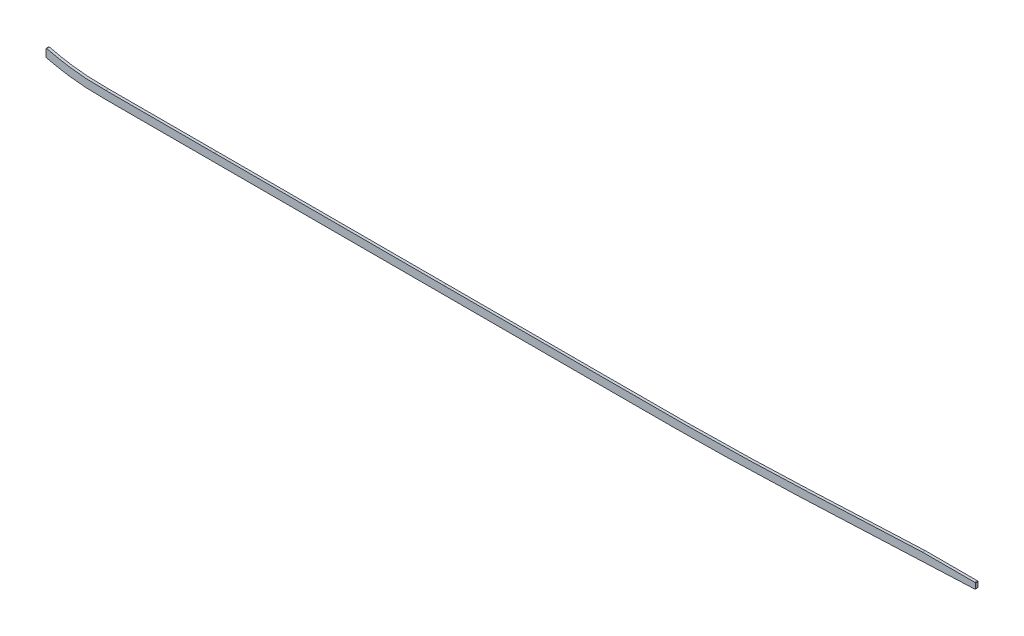
SolidWorks part; units mm, degrees
material "Plywood"
ref_plane "Front Plane" through (0, 0, 0) normal (0, 0, 1) x (1, 0, 0)
ref_plane "Top Plane" through (0, 0, 0) normal (0, 1, 0) x (1, 0, 0)
ref_plane "Right Plane" through (0, 0, 0) normal (1, 0, 0) x (0, 0, -1)
sketch "Sketch1" plane through (0, 0, 0) normal (0, 0, 1) x (1, 0, 0)
  line L0 (1046.2855, 53.4707) -> (499.61, 53.4707) construction
  line L1 (55, 0) -> (-55, 0) construction
  line L2 (1046.2855, -53.4707) -> (499.61, -53.4707)
  line L3 (1046.2855, -34.4207) -> (499.61, -34.4207)
  line L4 (99.06, -18.1493) -> (99.06, -37.7415)
  line L5 (2669.54, 9.5231) -> (2669.54, -9.569)
  spline S0 degree 5 poles (2699.7923, 7.5245) (2639.6368, 11.6572) (2579.4813, 15.4358) (2518.4981, 19.1485) (2436.3555, 23.2524) (2354.213, 26.6315) (2332.5703, 27.481) (2156.2686, 34.3778) (1979.9669, 41.6286) (1824.1143, 52.7713) (1636.9286, 53.5796) (1449.7429, 53.454) (1418.0067, 53.4707) (1324.8993, 53.4707) (1231.7919, 53.4707) (1170.4413, 53.4707) (1108.7841, 53.4707) (1047.1269, 53.4707) (1046.8464, 53.4707) (1046.5659, 53.4707) (1046.2855, 53.4707) knots 100.654805 100.654805 100.654805 100.654805 100.654805 100.654805 130.927897 130.927897 130.927897 141.337055 141.337055 141.337055 218.101815 218.101815 218.101815 233.772059 233.772059 233.772059 264.077723 264.077723 264.077723 264.216209 264.216209 264.216209 264.216209 264.216209 264.216209 weights 1 1 1 1 1 1 1 1 1 1 1 1 1 1 1 1 1 1 1 1 1 construction
  spline S1 degree 5 poles (499.61, 53.4707) (492.1368, 53.4707) (484.7543, 53.4707) (477.443, 53.4707) (448.5166, 53.4707) (419.5901, 53.4707) (398.3681, 53.4707) (355.6475, 53.4707) (312.927, 53.4707) (289.2351, 53.4703) (265.365, 53.4707) (241.4948, 53.4707) (241.4716, 53.4707) (241.4484, 53.4707) (241.4251, 53.4707) knots 19.90683 19.90683 19.90683 19.90683 19.90683 19.90683 23.637897 23.637897 23.637897 34.276546 34.276546 34.276546 46.401341 46.401341 46.401341 46.413154 46.413154 46.413154 46.413154 46.413154 46.413154 weights 1 1 1 1 1 1 1 1 1 1 1 1 1 1 1 construction
  spline S2 degree 5 poles (241.4251, 53.4707) (224.2869, 53.4707) (207.1495, 53.4673) (190.2039, 52.6866) (151.6561, 49.0319) (113.1083, 41.5037) (91.9499, 36.3426) (71.313, 30.9696) (50.6762, 24.7565) knots 0 0 0 0 0 0 8.713816 8.713816 8.713816 19.90683 19.90683 19.90683 19.90683 19.90683 19.90683 weights 1 1 1 1 1 1 1 1 1 construction
  spline S3 degree 5 poles (241.4251, -53.4707) (224.2869, -53.4707) (207.1495, -53.4673) (190.2039, -52.6866) (151.6561, -49.0319) (113.1083, -41.5037) (91.9499, -36.3426) (71.313, -30.9696) (50.6762, -24.7565) knots 0 0 0 0 0 0 8.713816 8.713816 8.713816 19.90683 19.90683 19.90683 19.90683 19.90683 19.90683 weights 1 1 1 1 1 1 1 1 1
  spline S4 degree 5 poles (499.61, -53.4707) (492.1368, -53.4707) (484.7543, -53.4707) (477.443, -53.4707) (448.5166, -53.4707) (419.5901, -53.4707) (398.3681, -53.4707) (355.6475, -53.4707) (312.927, -53.4707) (289.2351, -53.4703) (265.365, -53.4707) (241.4948, -53.4707) (241.4716, -53.4707) (241.4484, -53.4707) (241.4251, -53.4707) knots 19.90683 19.90683 19.90683 19.90683 19.90683 19.90683 23.637897 23.637897 23.637897 34.276546 34.276546 34.276546 46.401341 46.401341 46.401341 46.413154 46.413154 46.413154 46.413154 46.413154 46.413154 weights 1 1 1 1 1 1 1 1 1 1 1 1 1 1 1
  spline S5 degree 5 poles (2699.7923, -7.5245) (2639.6368, -11.6572) (2579.4813, -15.4358) (2518.4981, -19.1485) (2436.3555, -23.2524) (2354.213, -26.6315) (2332.5703, -27.481) (2156.2686, -34.3778) (1979.9669, -41.6286) (1824.1143, -52.7713) (1636.9286, -53.5796) (1449.7429, -53.454) (1418.0067, -53.4707) (1324.8993, -53.4707) (1231.7919, -53.4707) (1170.4413, -53.4707) (1108.7841, -53.4707) (1047.1269, -53.4707) (1046.8464, -53.4707) (1046.5659, -53.4707) (1046.2855, -53.4707) knots 100.654805 100.654805 100.654805 100.654805 100.654805 100.654805 130.927897 130.927897 130.927897 141.337055 141.337055 141.337055 218.101815 218.101815 218.101815 233.772059 233.772059 233.772059 264.077723 264.077723 264.077723 264.216209 264.216209 264.216209 264.216209 264.216209 264.216209 weights 1 1 1 1 1 1 1 1 1 1 1 1 1 1 1 1 1 1 1 1 1
  spline S6 degree 1 poles (2698.4867, 11.4807) (1046.2855, -34.4207) knots 0 0 1 1 construction
  spline S7 degree 1 poles (499.61, -34.4207) (241.4252, -34.4207) knots 0 0 1 1 construction
  spline S8 degree 1 poles (241.4252, -34.4207) (56.168, -6.5153) knots 0 0 1 1 construction
  spline S9 degree 3 poles (2698.4867, 11.4807) (2691.2474, 10.9833) (2679.1952, 10.1655) (2662.2765, 9.0388) (2635.6663, 7.2925) (2596.8577, 4.8261) (2545.7297, 1.7583) (2494.4053, -1.0986) (2451.533, -3.2666) (2417.1983, -4.8671) (2391.4571, -6.0036) (2365.6347, -7.0869) (2339.5463, -8.1377) (2313.4661, -9.1651) (2287.6124, -10.1795) (2261.7633, -11.201) (2227.2853, -12.5838) (2184.1756, -14.3661) (2132.4291, -16.6074) (2063.4255, -19.7089) (1977.1749, -23.7005) (1873.7325, -28.1494) (1770.3746, -31.6575) (1667.0857, -33.7931) (1581.0111, -34.3832) (1512.074, -34.4278) (1443.0615, -34.4095) (1356.8009, -34.4244) (1218.7946, -34.4185) (1115.289, -34.4207) (1046.2855, -34.4207) knots 100.654805 100.654805 100.654805 100.654805 102.842388 104.300777 105.766098 110.877392 115.988686 121.09998 126.211274 128.766921 131.322568 133.878215 136.433862 138.989509 141.545156 144.100803 146.656449 151.767743 156.879037 161.990331 172.212919 182.435507 192.658094 202.880682 213.10327 218.214564 223.325858 233.548445 243.771033 264.216209 264.216209 264.216209 264.216209
  spline S10 degree 3 poles (499.61, -34.4207) (488.6147, -34.4207) (472.2364, -34.4207) (449.9402, -34.4207) (427.7713, -34.4207) (405.8747, -34.4207) (384.5849, -34.4207) (368.9002, -34.4207) (353.3766, -34.4207) (332.6085, -34.4207) (306.2878, -34.4206) (274.0235, -34.4205) (252.271, -34.4207) (241.4252, -34.4207) knots 19.90683 19.90683 19.90683 19.90683 23.22012 24.876765 26.533411 29.846701 31.503346 33.159992 34.816637 36.473282 39.786573 43.099863 46.413154 46.413154 46.413154 46.413154
  spline S11 degree 3 poles (241.4252, -34.4207) (239.3949, -34.4207) (235.3223, -34.4205) (227.2744, -34.3987) (217.3194, -34.2975) (205.5307, -33.9764) (189.9633, -33.2126) (170.697, -31.5435) (147.5333, -28.3144) (125.4828, -24.2021) (107.4399, -20.1965) (92.2061, -16.4882) (75.9505, -12.2555) (63.6202, -8.7589) (56.168, -6.5153) knots 0 0 0 0 0.622088 1.244177 2.488354 3.732531 4.976707 7.465061 9.953415 12.441768 14.558235 15.802412 17.418476 19.90683 19.90683 19.90683 19.90683
  point P2 (0, 0)
  dimension "D1" = 50.6762
  dimension "D3" = 99.06
  dimension "D4" = 2669.54
  dimension "D2" = 19.05
extrude "Boss-Extrude1" add sketch "Sketch1" along normal mid plane 6.35 contours S10 S11 L4 S3 S4 L2 S5 L5 S9 L3
sketch "Sketch2" plane through (0, 0, 3.175) normal (0, 0, 1) x (1, 0, 0)
  line L0 (2185.533, -14.3257) -> (2311.4, -14.3257)
  line L1 (2311.4, -14.3257) -> (2311.4, -9.2457)
  line L2 (2311.4, -14.3257) -> (2311.4, -28.3104)
  line L3 (2669.54, 9.5231) -> (2669.54, -9.569) construction
  line L4 (2669.54, 9.5231) -> (2669.54, -9.569)
  spline S0 degree 3 poles (689.0175, 232.3189) (4033.8285, 148.9311) (3356.6623, 54.6077) (2635.6663, 7.2925) (2596.8577, 4.8261) (2545.7297, 1.7583) (2494.4053, -1.0986) (2451.533, -3.2666) (2417.1983, -4.8671) (2391.4571, -6.0036) (2365.6347, -7.0869) (2339.5463, -8.1377) (2313.4661, -9.1651) (2287.6124, -10.1795) (2261.7633, -11.201) (2227.2853, -12.5838) (2184.1756, -14.3661) (2132.4291, -16.6074) (2063.4255, -19.7089) (1977.1749, -23.7005) (1873.7325, -28.1494) (1770.3746, -31.6575) (1667.0857, -33.7931) (1581.0111, -34.3832) (1512.074, -34.4278) (1443.0615, -34.4095) (1356.8009, -34.4244) (551.9641, -34.3896) (-218.4198, -34.7282) (-953.6342, -29.9632) knots -106.828462 -106.828462 -106.828462 -106.828462 104.300777 105.766098 110.877392 115.988686 121.09998 126.211274 128.766921 131.322568 133.878215 136.433862 138.989509 141.545156 144.100803 146.656449 151.767743 156.879037 161.990331 172.212919 182.435507 192.658094 202.880682 213.10327 218.214564 223.325858 233.548445 243.771033 461.793666 461.793666 461.793666 461.793666 only from (2669.54, 9.5231) to (1046.2855, -34.4207) construction
  spline S1 degree 3 poles (2669.54, 9.5231) (2667.1265, 9.3624) (2659.8616, 8.8803) (2635.6663, 7.2925) (2596.8577, 4.8261) (2545.7297, 1.7583) (2494.4053, -1.0986) (2451.533, -3.2666) (2417.1983, -4.8671) (2391.4571, -6.0036) (2365.6347, -7.0869) (2339.5463, -8.1377) (2313.4661, -9.1651) (2287.6124, -10.1795) (2261.7633, -11.201) (2227.2853, -12.5838) (2184.1756, -14.3661) (2132.4291, -16.6074) (2063.4255, -19.7089) (1977.1749, -23.7005) (1873.7325, -28.1494) (1770.3746, -31.6575) (1667.0857, -33.7931) (1581.0111, -34.3832) (1512.074, -34.4278) (1443.0615, -34.4095) (1356.8009, -34.4244) (1218.7946, -34.4185) (1115.289, -34.4207) (1046.2855, -34.4207) knots 103.571583 103.571583 103.571583 103.571583 104.300777 105.766098 110.877392 115.988686 121.09998 126.211274 128.766921 131.322568 133.878215 136.433862 138.989509 141.545156 144.100803 146.656449 151.767743 156.879037 161.990331 172.212919 182.435507 192.658094 202.880682 213.10327 218.214564 223.325858 233.548445 243.771033 264.216209 264.216209 264.216209 264.216209
  spline S2 degree 5 poles (4524.4896, 699.6349) (3179.77, -69.42) (3083.4624, 36.6115) (2859.542, 1.0131) (2606.8775, -16.2376) (2354.213, -26.6315) (2332.5703, -27.481) (2156.2686, -34.3778) (1979.9669, -41.6286) (1824.1143, -52.7713) (1636.9286, -53.5796) (1449.7429, -53.454) (1418.0067, -53.4707) (1324.8993, -53.4707) (1231.7919, -53.4707) (1170.4413, -53.4707) (970.3038, -53.4707) (770.1663, -53.4707) (702.0423, -53.4707) (-16.6162, -53.4711) (3039.7057, -53.1927) knots 16.201417 16.201417 16.201417 16.201417 16.201417 16.201417 130.927897 130.927897 130.927897 141.337055 141.337055 141.337055 218.101815 218.101815 218.101815 233.772059 233.772059 233.772059 264.077723 264.077723 264.077723 332.592886 332.592886 332.592886 332.592886 332.592886 332.592886 weights 1 1 1 1 1 1 1 1 1 1 1 1 1 1 1 1 1 1 1 1 1 only from (2669.54, -9.569) to (1046.2855, -53.4707) construction
  spline S3 degree 5 poles (2669.54, -9.569) (2615.3936, -13.1707) (2561.0807, -16.5361) (2506.2052, -19.7586) (2430.2091, -23.5052) (2354.213, -26.6315) (2332.5703, -27.481) (2156.2686, -34.3778) (1979.9669, -41.6286) (1824.1143, -52.7713) (1636.9286, -53.5796) (1449.7429, -53.454) (1418.0067, -53.4707) (1324.8993, -53.4707) (1231.7919, -53.4707) (1170.4413, -53.4707) (1108.7841, -53.4707) (1047.1269, -53.4707) (1046.8464, -53.4707) (1046.5659, -53.4707) (1046.2855, -53.4707) knots 103.698914 103.698914 103.698914 103.698914 103.698914 103.698914 130.927897 130.927897 130.927897 141.337055 141.337055 141.337055 218.101815 218.101815 218.101815 233.772059 233.772059 233.772059 264.077723 264.077723 264.077723 264.216209 264.216209 264.216209 264.216209 264.216209 264.216209 weights 1 1 1 1 1 1 1 1 1 1 1 1 1 1 1 1 1 1 1 1 1
  point P2 (0, 0)
  spline M7 degree 5 poles (1046.2855, -53.4707) (1046.5659, -53.4707) (1046.8464, -53.4707) (1047.1269, -53.4707) (1108.7841, -53.4707) (1170.4413, -53.4707) (1231.7919, -53.4707) (1324.8993, -53.4707) (1418.0067, -53.4707) (1449.7429, -53.454) (1636.9286, -53.5796) (1824.1143, -52.7713) (1979.9669, -41.6286) (2156.2686, -34.3778) (2332.5703, -27.481) (2354.213, -26.6315) (2436.3555, -23.2524) (2518.4981, -19.1485) (2579.4813, -15.4358) (2639.6368, -11.6572) (2699.7923, -7.5245) knots 100.654805 100.654805 100.654805 100.654805 100.654805 100.654805 100.79329 100.79329 100.79329 131.098954 131.098954 131.098954 146.769198 146.769198 146.769198 223.533959 223.533959 223.533959 233.943117 233.943117 233.943117 264.216209 264.216209 264.216209 264.216209 264.216209 264.216209 weights 1 1 1 1 1 1 1 1 1 1 1 1 1 1 1 1 1 1 1 1 1 only from (1046.2855, -53.4707) to (2669.54, -9.569)
  line M8 (2669.54, -9.569) -> (2669.54, 9.5231)
  spline M9 degree 3 poles (2698.4867, 11.4807) (2691.2474, 10.9833) (2679.1952, 10.1655) (2662.2765, 9.0388) (2635.6663, 7.2925) (2596.8577, 4.8261) (2545.7297, 1.7583) (2494.4053, -1.0986) (2451.533, -3.2666) (2417.1983, -4.8671) (2391.4571, -6.0036) (2365.6347, -7.0869) (2339.5463, -8.1377) (2313.4661, -9.1651) (2287.6124, -10.1795) (2261.7633, -11.201) (2227.2853, -12.5838) (2184.1756, -14.3661) (2132.4291, -16.6074) (2063.4255, -19.7089) (1977.1749, -23.7005) (1873.7325, -28.1494) (1770.3746, -31.6575) (1667.0857, -33.7931) (1581.0111, -34.3832) (1512.074, -34.4278) (1443.0615, -34.4095) (1356.8009, -34.4244) (1218.7946, -34.4185) (1115.289, -34.4207) (1046.2855, -34.4207) knots 100.654805 100.654805 100.654805 100.654805 102.842388 104.300777 105.766098 110.877392 115.988686 121.09998 126.211274 128.766921 131.322568 133.878215 136.433862 138.989509 141.545156 144.100803 146.656449 151.767743 156.879037 161.990331 172.212919 182.435507 192.658094 202.880682 213.10327 218.214564 223.325858 233.548445 243.771033 264.216209 264.216209 264.216209 264.216209 only from (2669.54, 9.5231) to (1046.2855, -34.4207)
  dimension "D1" = 2311.4
  dimension "D2" = 5.08
extrude "Cut-Extrude1" cut sketch "Sketch2" against normal through all contours L0 L1 M9 | L1 L2 M7 M8 M9
fillet "Fillet1" radius 1.27 4 edges at (99.06, -37.7415, 0) (99.06, -18.1493, 0)
